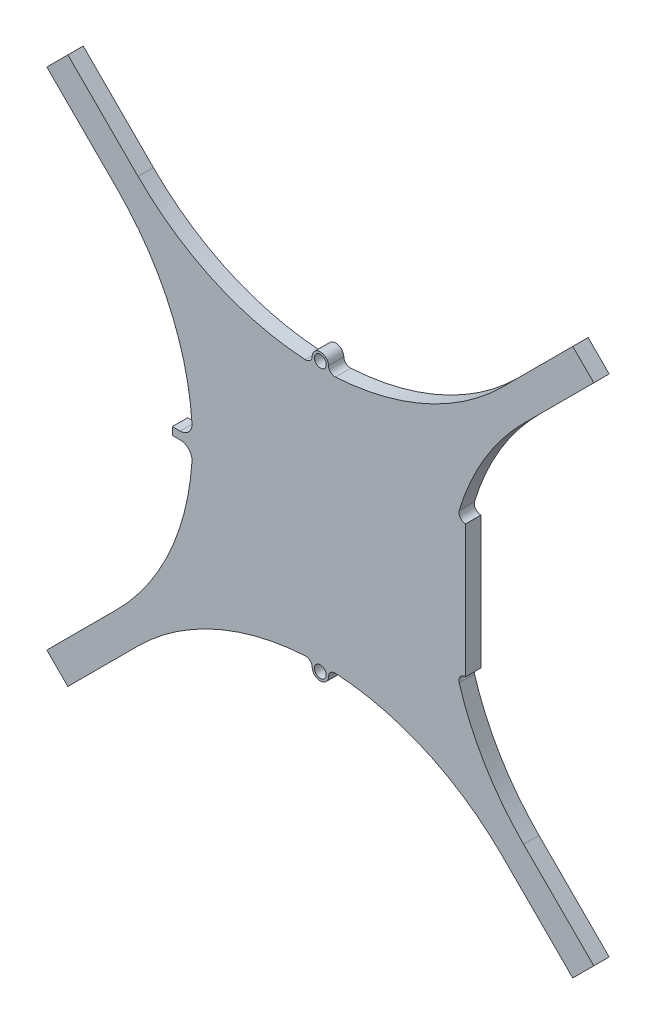
SolidWorks part; units mm, degrees
ref_plane "Front Plane" through (0, 0, 0) normal (0, 0, 1) x (1, 0, 0)
ref_plane "Top Plane" through (0, 0, 0) normal (0, 1, 0) x (1, 0, 0)
ref_plane "Right Plane" through (0, 0, 0) normal (1, 0, 0) x (0, 0, -1)
sketch "Sketch1" plane through (0, 0, 0) normal (0, 0, 1) x (1, 0, 0)
  line L0 (-27.1352, 29.398) -> (-29.398, 27.1352)
  line L1 (-21.8551, 19.5923) -> (-29.398, 27.1352)
  line L2 (-21.8551, -19.5923) -> (-29.398, -27.1352)
  line L3 (29.398, 27.1352) -> (27.1352, 29.398)
  line L4 (0, 0) -> (0, -41.4474) construction
  line L5 (19.5923, 21.8551) -> (27.1352, 29.398)
  line L6 (-19.5923, 21.8551) -> (-27.1352, 29.398)
  line L7 (27.1352, -29.398) -> (29.398, -27.1352)
  line L8 (21.8551, -19.5923) -> (29.398, -27.1352)
  line L9 (21.8551, 19.5923) -> (29.398, 27.1352)
  line L10 (19.5923, -21.8551) -> (27.1352, -29.398)
  line L11 (0, 0) -> (0, 41.4474) construction
  line L12 (-29.398, -27.1352) -> (-27.1352, -29.398)
  line L13 (0, 0) -> (-15.9085, 0) construction
  line L14 (15.6189, 7.115) -> (15.6189, -7.115)
  line L15 (0, 0) -> (33.3791, 33.3791) construction
  line L16 (15.6189, 7.115) -> (14.6688, 7.115)
  line L17 (-19.5923, -21.8551) -> (-27.1352, -29.398)
  line L18 (15.6189, -7.115) -> (14.6688, -7.115)
  line L19 (-15.9085, -0.4114) -> (-13.7427, -0.4114)
  line L20 (-15.9085, -0.4114) -> (-15.9085, 0.4114)
  line L21 (-15.9085, 0.4114) -> (-13.7427, 0.4114)
  arc A0 (19.5923, -21.8551) -> (0.5189, -13.7445) centre (0, -41.4474) ccw
  arc A1 (-21.8551, -19.5923) -> (-13.7427, -0.4114) centre (-41.4474, 0) ccw
  arc A2 (-19.5923, 21.8551) -> (-0.5189, 13.7445) centre (0, 41.4474) ccw
  arc A3 (21.8551, 19.5923) -> (14.6688, 7.115) centre (41.4474, 0) ccw
  arc A4 (0.5189, 13.7445) -> (-0.5189, 13.7445) centre (0, 14.4491) ccw
  circle A5 centre (0, 14.4491) radius 0.6348
  arc A6 (0.5189, 13.7445) -> (19.5923, 21.8551) centre (0, 41.4474) ccw
  circle A7 centre (0, -14.4491) radius 0.6348
  arc A8 (0.5189, -13.7445) -> (-0.5189, -13.7445) centre (0, -14.4491) cw
  arc A9 (-0.5189, -13.7445) -> (-19.5923, -21.8551) centre (0, -41.4474) ccw
  arc A10 (14.6688, -7.115) -> (21.8551, -19.5923) centre (41.4474, 0) ccw
  arc A11 (-13.7427, 0.4114) -> (-21.8551, 19.5923) centre (-41.4474, 0) ccw
  point P17 (0, 0)
  point P32 (0, 0)
  point P33 (0, 0)
  point P39 (15.6189, 0)
  dimension "D2" = 27.7077
  dimension "D10" = 1.75
  dimension "D11" = 14.4491
  dimension "D12" = 0.2402
  dimension "D1" = 41.4474
  dimension "D3" = 4
  dimension "D4" = 135
  dimension "D5" = 4
  dimension "D6" = 10.6673
  dimension "D7" = 3.2
  dimension "D8" = 39.975
  dimension "D13" = 15.6189
  dimension "D14" = 7.115
  dimension "D15" = 0.4114
  dimension "D16" = 2.1658
  dimension "D9" = 4
extrude "Boss-Extrude1" add sketch "Sketch1" along normal blind 1.65
fillet "Fillet1" radius 0.7112 4 edges at (-0.5189, -13.7445, 0.825) (0.5189, -13.7445, 0.825) (-0.5189, 13.7445, 0.825) (0.5189, 13.7445, 0.825)
fillet "Fillet2" radius 0.7112 2 edges at (14.6688, -7.115, 0.825) (14.6688, 7.115, 0.825)
fillet "Fillet3" radius 1.27 2 edges at (-13.7427, 0.4114, 0.825) (-13.7427, -0.4114, 0.825)
